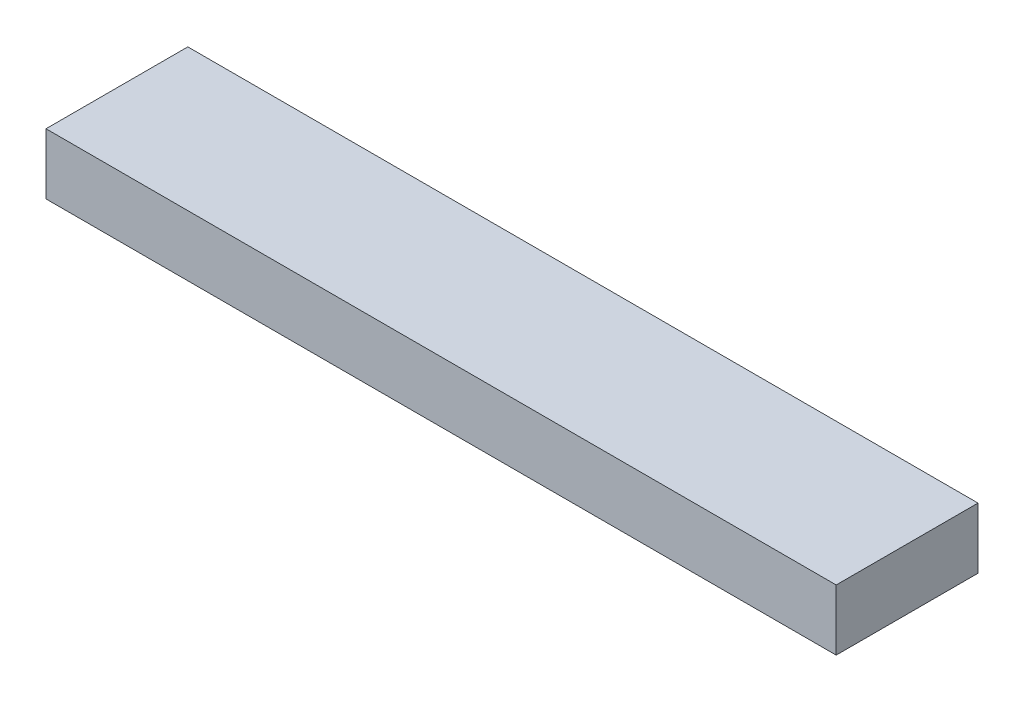
SolidWorks part; units mm, degrees
ref_plane "Front Plane" through (0, 0, 0) normal (0, 0, 1) x (1, 0, 0)
ref_plane "Top Plane" through (0, 0, 0) normal (0, 1, 0) x (1, 0, 0)
ref_plane "Right Plane" through (0, 0, 0) normal (1, 0, 0) x (0, 0, -1)
sketch "Sketch1" plane through (0, 0, 0) normal (0, 1, 0) x (1, 0, 0)
  line L1 (0, 0) -> (495.3, 0)
  line L2 (0, 0) -> (0, 88.9)
  line L3 (0, 88.9) -> (495.3, 88.9)
  line L4 (495.3, 0) -> (495.3, 88.9)
  dimension "D1" = 88.9
  dimension "D2" = 495.3
extrude "Boss-Extrude1" add sketch "Sketch1" along normal blind 38.1
